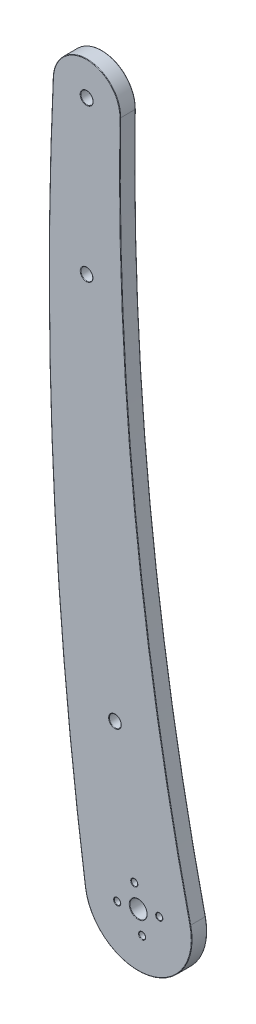
SolidWorks part; units mm, degrees
ref_plane "Front Plane" through (0, 0, 0) normal (0, 0, 1) x (1, 0, 0)
ref_plane "Top Plane" through (0, 0, 0) normal (0, 1, 0) x (1, 0, 0)
ref_plane "Right Plane" through (0, 0, 0) normal (1, 0, 0) x (0, 0, -1)
sketch "Sketch1" plane through (0, 0, 0) normal (0, 0, 1) x (1, 0, 0)
  line L0 (-20.22, 57.58) -> (-37.0777, 278.939) construction
  line L1 (-20.22, 57.58) -> (-37.0777, 278.939) construction
  line L2 (-20.22, 57.58) -> (-17.0242, 40.3743) construction
  line L3 (-20.22, 57.58) -> (-3.0143, 60.7758) construction
  line L4 (-20.22, 57.58) -> (-23.4158, 74.7857) construction
  line L5 (-20.22, 57.58) -> (-37.4257, 54.3842) construction
  circle A0 centre (-37.0777, 278.939) radius 11 construction
  circle A1 centre (-37.0777, 278.939) radius 11 construction
  circle A2 centre (-20.22, 57.58) radius 17.5 construction
  circle A3 centre (-20.22, 57.58) radius 17.5 construction
  circle A4 centre (-20.22, 57.58) radius 2.8
  circle A5 centre (-37.0777, 278.939) radius 2
  arc A8 (-26.0792, 278.7566) -> (-3.1679, 61.514) centre (873.7971, 263.8316) ccw
  arc A9 (-48.0656, 279.4542) -> (-37.5474, 55.1282) centre (1150.6174, 223.2484) ccw
  arc A10 (-37.0777, 278.939) -> (-20.22, 57.58) centre (1087.6295, 253.27) ccw construction
  arc A11 (-48.0656, 279.4542) -> (-26.0792, 278.7566) centre (-37.0777, 278.939) cw
  arc A12 (-37.5474, 55.1282) -> (-3.1679, 61.514) centre (-20.22, 57.58) ccw
  circle A13 centre (-37.1074, 228.939) radius 1.95
  circle A15 centre (-27.821, 106.9989) radius 1.95
  circle A17 centre (-18.9417, 50.6977) radius 1.05
  circle A18 centre (-27.1023, 56.3017) radius 1.05
  circle A19 centre (-21.4983, 64.4623) radius 1.05
  circle A20 centre (-13.3377, 58.8583) radius 1.05
  point P19 (-37.1074, 228.939)
  point P20 (-27.821, 106.9989)
  dimension "D1" = 4
  dimension "D2" = 5.6
  dimension "D3" = 1200
  dimension "D4" = 1125
  dimension "D5" = 900
  dimension "D8" = 3.9
  dimension "D9" = 2.1
  dimension "D6" = 50
  dimension "D7" = 50
  dimension "D10" = 7
  dimension "D11" = 7
extrude "Boss-Extrude1" add sketch "Sketch1" against normal blind 5
fillet "Fillet1" radius 0.15 24 edges at (-48.0657, 167.0447, -5) (-17.0242, 40.3743, -5) (-21.2391, 169.4376, -5) (-36.7288, 289.9335, -5) (-17.42, 57.58, -5) (-35.0777, 278.939, -5) (-25.871, 106.9989, -5) (-35.1574, 228.939, -5) (-21.2391, 169.4376, 0) (-17.0242, 40.3743, 0) (-48.0657, 167.0447, 0) (-36.7288, 289.9335, 0) (-17.42, 57.58, 0) (-35.0777, 278.939, 0) (-25.871, 106.9989, 0) (-35.1574, 228.939, 0) (-17.8917, 50.6977, -5) (-17.8917, 50.6977, 0) (-26.0523, 56.3017, -5) (-26.0523, 56.3017, 0) (-22.5483, 64.4623, -5) (-14.3877, 58.8583, -5) (-22.5483, 64.4623, 0) (-14.3877, 58.8583, 0)
